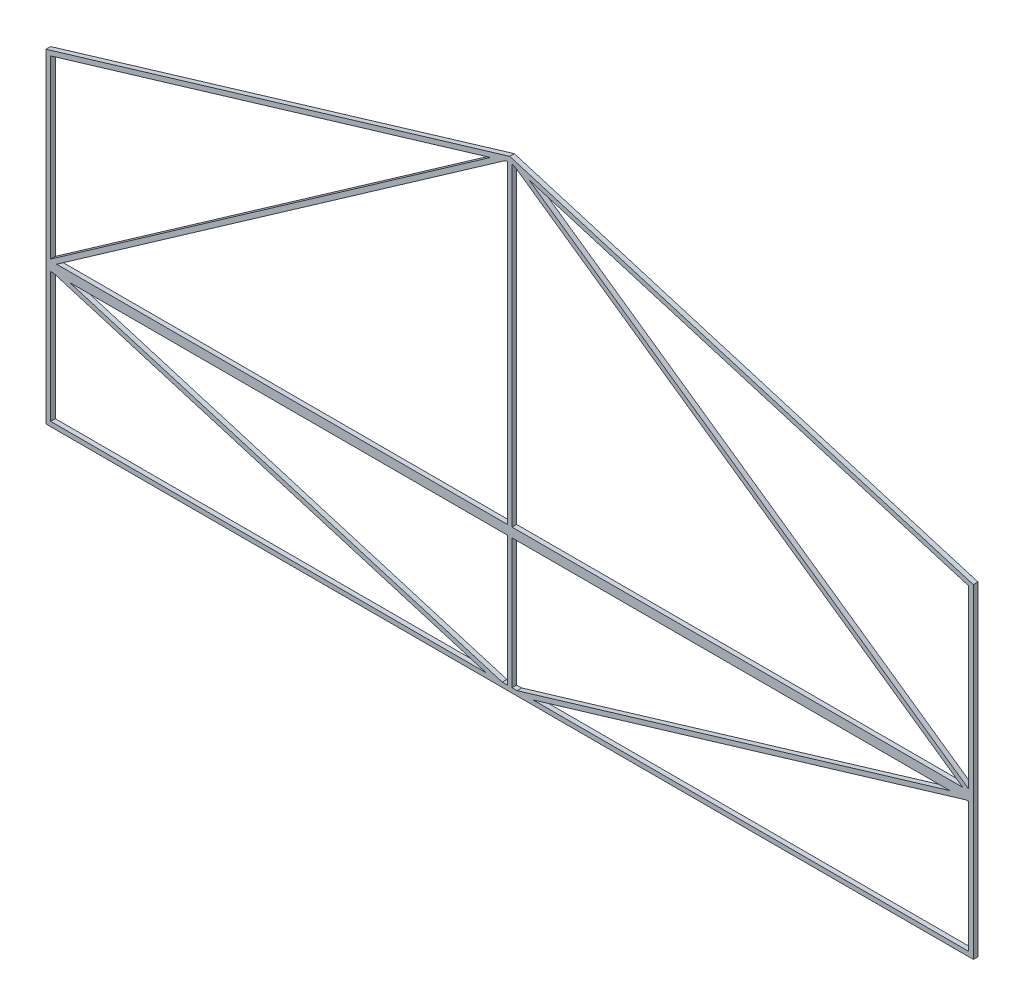
SolidWorks part; units mm, degrees
material "ﾊﾞﾙｻ"
ref_plane "正面" through (0, 0, 0) normal (0, 0, 1) x (1, 0, 0)
ref_plane "平面" through (0, 0, 0) normal (0, 1, 0) x (1, 0, 0)
ref_plane "右側面" through (0, 0, 0) normal (1, 0, 0) x (0, 0, -1)
sketch "Model" plane through (0, 0, 0) normal (0, 0, 1) x (1, 0, 0)
  line L0 (0, 0) -> (400, 0)
  line L1 (400, 0) -> (400, 58.956)
  line L2 (0, 60) -> (0, 58.956)
  line L3 (200, 200) -> (201, 199.7)
  line L4 (200, 60) -> (396.5199, 60)
  line L5 (200, 60) -> (0, 60)
  line L6 (0, 61.2207) -> (0, 60)
  line L7 (400, 61.2207) -> (400, 140)
  line L8 (2, 2) -> (2, 58)
  line L9 (2, 58) -> (3.1866, 58)
  line L10 (3.1866, 58) -> (189.8532, 2)
  line L11 (189.8532, 2) -> (2, 2)
  line L12 (398, 58) -> (398, 2)
  line L13 (398, 2) -> (210.1468, 2)
  line L14 (210.1468, 2) -> (396.8134, 58)
  line L15 (396.8134, 58) -> (398, 58)
  line L16 (191.7282, 195.4304) -> (2, 62.6207)
  line L17 (2, 62.6207) -> (2, 138.5119)
  line L18 (2, 138.5119) -> (191.7282, 195.4304)
  line L19 (197.8315, 197.2614) -> (4.6009, 62)
  line L20 (4.6009, 62) -> (199, 62)
  line L21 (199, 62) -> (199, 197.6119)
  line L22 (199, 197.6119) -> (197.8315, 197.2614)
  line L23 (201, 2) -> (201, 58)
  line L24 (201, 58) -> (389.8532, 58)
  line L25 (389.8532, 58) -> (203.1866, 2)
  line L26 (203.1866, 2) -> (201, 2)
  line L27 (199, 2) -> (199, 58)
  line L28 (199, 58) -> (10.1468, 58)
  line L29 (10.1468, 58) -> (196.8134, 2)
  line L30 (196.8134, 2) -> (199, 2)
  line L31 (201, 62) -> (201, 197.6119)
  line L32 (201, 197.6119) -> (202.1685, 197.2614)
  line L33 (202.1685, 197.2614) -> (395.3991, 62)
  line L34 (395.3991, 62) -> (201, 62)
  line L35 (0, 140) -> (0, 61.2207)
  line L36 (0, 58.956) -> (0, 0)
  line L37 (0, 140) -> (196.9484, 199.0845)
  line L38 (199, 199.7) -> (200, 200)
  line L39 (196.9484, 199.0845) -> (199, 199.7)
  line L40 (203.0516, 199.0845) -> (400, 140)
  line L41 (398, 138.5119) -> (208.2718, 195.4304)
  line L42 (208.2718, 195.4304) -> (398, 62.6207)
  line L43 (398, 62.6207) -> (398, 138.5119)
  line L44 (201, 199.7) -> (203.0516, 199.0845)
  line L45 (396.5199, 60) -> (400, 60)
  line L46 (400, 60) -> (400, 61.2207)
  line L47 (400, 58.956) -> (400, 60)
extrude "ﾎﾞｽ - 押し出し1" add sketch "Model" along normal blind 2 contours L45 L46 L7 L40 L44 L3 L38 L39 L37 L35 L6 L5 L4 L33 L34 L31 L32 L17 L18 L16 L22 L21 L20 L19 L43 L42 L41 | L1 L47 L45 L4 L5 L2 L36 L0 L25 L26 L23 L24 L14 L15 L12 L13 L10 L11 L8 L9 L30 L29 L28 L27
